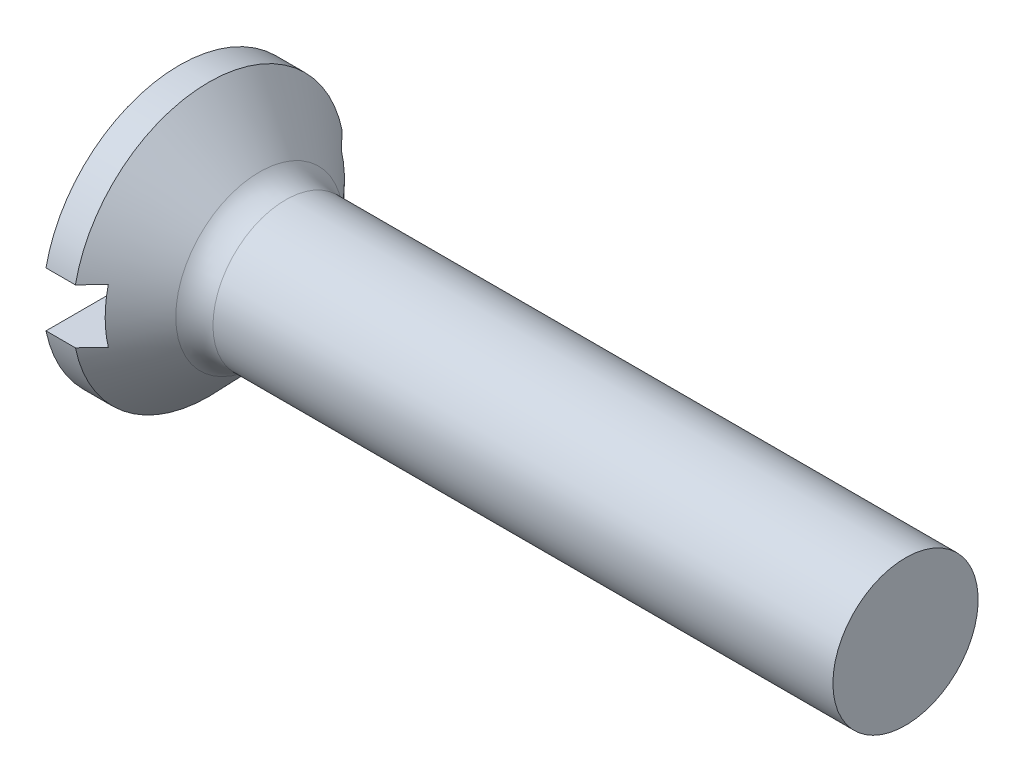
SolidWorks part; units mm, degrees
ref_plane "Front Plane" through (0, 0, 0) normal (0, 0, 1) x (1, 0, 0)
ref_plane "Top Plane" through (0, 0, 0) normal (0, 1, 0) x (1, 0, 0)
ref_plane "Right Plane" through (0, 0, 0) normal (1, 0, 0) x (0, 0, -1)
sketch "BodySke" plane through (0, 0, 0) normal (0, 0, 1) x (1, 0, 0)
  line L0 (0, 0) -> (111.3824, 0) construction
  line L1 (0, 0) -> (0, 1.5)
  line L2 (0, 1.5) -> (0.324, 1.5)
  line L3 (0.324, 1.5) -> (1, 0.8)
  line L4 (1, 0.8) -> (8, 0.8)
  line L5 (8, 0.8) -> (8, 0)
  line L6 (1.35, 4.624) -> (1.35, -10.0939) construction
  line L7 (0, 0) -> (8, 0)
  line L8 (1.7, 4.624) -> (1.7, -9.158) construction
  line L9 (0, -1.5) -> (0.324, -1.5) construction
  line L10 (0.324, -1.5) -> (1, -0.8) construction
  line L11 (1, -0.8) -> (8, -0.8) construction
  point P10 (8, 0.601)
  dimension "Thread_minor" = 1.202
  dimension "Diameter" = 1.6
  dimension "Length" = 8
  dimension "Head_ang" = 92
  dimension "Head_height" = 1
  dimension "Head_dia" = 3
  dimension "Advance" = 0.35
  dimension "Thread_runout" = 0.7
revolve "BaseBody" add sketch "BodySke" angle 360 about L0
cosmetic thread "ThreadCosmetic" [suppressed] parameters "Thread_minor"=1.202
fillet "Fillet1" radius 0.4 1 edges at (1, 0, 0.8)
sketch "SlotSke" plane through (0, 0, 0) normal (-1, 0, 0) x (0, 0, 1)
  line L1 (-1.5, 0.3) -> (1.5, 0.3)
  line L2 (-1.5, 0.3) -> (-1.5, -0.3)
  line L3 (-1.5, -0.3) -> (1.5, -0.3)
  line L4 (1.5, 0.3) -> (1.5, -0.3)
  dimension "D1" = 3
  dimension "D2" = 1.5
  dimension "Slot_width" = 0.6
  dimension "D3" = 0.3
extrude "Slot" cut sketch "SlotSke" against normal blind 0.5
sketch "ThdSchSke" plane through (0, 0, 0) normal (0, 0, 1) x (1, 0, 0)
  line L0 (0, 0) -> (55.1256, 0) construction
  line L1 (0, 0) -> (111.3824, 0) construction
  line L2 (7.8851, 0.8) -> (7.8851, 1.0298)
  line L3 (7.8851, 1.0298) -> (8.1149, 1.0298)
  line L4 (8.1149, 1.0298) -> (8.1149, 0.8)
  line L5 (8.1149, 0.8) -> (8, 0.601)
  line L6 (8, 0.601) -> (7.8851, 0.8)
  line L7 (1, 0.8) -> (8, 0.8) construction
  line L13 (8, 0.8) -> (8, 0) construction
revolve "ThreadSchematic" [suppressed] cut sketch "ThdSchSke" angle 360 about L0
pattern_linear "ThdSchPat" [suppressed] count 19 along (1, 0, 0)
equation "\"Thread_minor@ThreadCosmetic\" = \"Thread_minor@BodySke\""
equation "\"D1@SlotSke\" = \"Head_dia@BodySke\""
equation "\"D2@SlotSke\" = \"D1@SlotSke\" / 2"
equation "\"D3@SlotSke\" = \"Slot_width@SlotSke\" / 2"
equation "\"Advance@ThdSchPat\" = \"Advance@BodySke\""
equation "\"D1@ThdSchPat\" =  int( ( \"Length@BodySke\" - \"Head_height@BodySke\" - \"Thread_runout@BodySke\" )  / \"Advance@ThdSchPat\" )   + 1"
